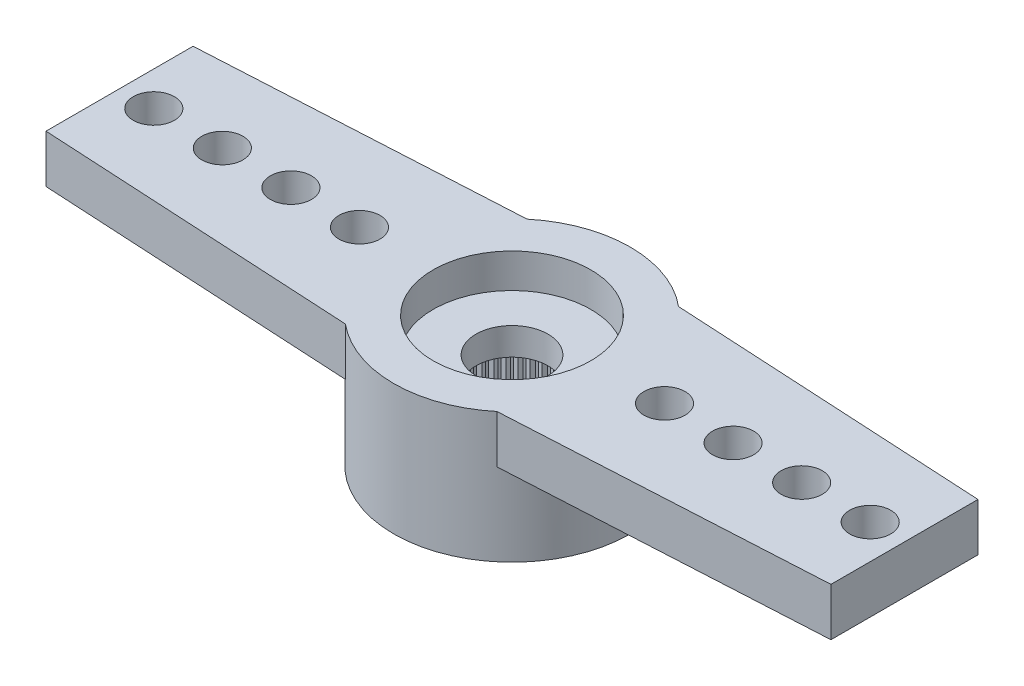
SolidWorks part; units mm, degrees
material "PVC Rígido"
ref_plane "Plano frontal" through (0, 0, 0) normal (0, 0, 1) x (1, 0, 0)
ref_plane "Plano superior" through (0, 0, 0) normal (0, 1, 0) x (1, 0, 0)
ref_plane "Plano direito" through (0, 0, 0) normal (1, 0, 0) x (0, 0, -1)
sketch "Esboço1" plane through (0, 0, 0) normal (0, 1, 0) x (1, 0, 0)
  line L0 (0, 0) -> (-14.05, 0) construction
  line L1 (-14.1591, 1.997) -> (-2.2091, 2.65)
  line L2 (-2.2091, -2.65) -> (-14.1591, -1.997)
  arc A0 (-2.2091, -2.65) -> (-2.2091, 2.65) centre (0, 0) ccw
  arc A1 (-14.1591, 1.997) -> (-14.1591, -1.997) centre (-14.05, 0) ccw
  dimension "D1" = 6.9
  dimension "D2" = 4
  dimension "D3" = 19.5
  dimension "D4" = 5.3
extrude "Ressalto-extrusão1" add sketch "Esboço1" against normal blind 1.4
sketch "Esboço2" plane through (0, -1.4, 0) normal (0, -1, 0) x (1, 0, 0)
  arc A0 (-2.2091, -2.65) -> (-2.2091, 2.65) centre (0, 0) ccw construction
  circle A1 centre (0, 0) radius 3.45
extrude "Ressalto-extrusão2" add sketch "Esboço2" along normal offset from surface (2.4 mm away) 3.8 up to face at (-7.242, 0, 0)
hole_wizard "Furo4" positions "Esboço9" profile "Esboço10" legacy end condition through all
sketch "Esboço9" plane through (0, 0, 0) normal (0, 1, 0) x (1, 0, 0)
  line L1 (-14.45, 0) -> (0, 0) construction
  arc A2 (-14.1591, 1.997) -> (-14.1591, -1.997) centre (-14.05, 0) ccw construction
  point P0 (-14.45, 0)
  point P19 (-16.05, 0)
  dimension "D1" = 1.6
sketch "Esboço10" plane through (-14.45, 0, 0) normal (1, 0, 0) x (0, 0, 1)
  line L0 (0, 0) -> (0, 3.8)
  line L1 (0, 3.8) -> (0.6, 3.8)
  line L2 (0.6, 3.8) -> (0.6, 0)
  line L3 (0.6, 0) -> (0, 0)
  line L4 (0, 110) -> (0, -10) construction
  dimension "Diameter" = 1.2
  dimension "Depth" = 3.8
pattern_linear "Padrão linear1" count 6 spacing 2 along (1, 0, 0) of "Furo4"
pattern_circular "PadrãoCircular2" count 2 over 360 about axis through (0, 0, 0) along (0, 1, 0) of "Ressalto-extrusão1", "Furo4", "Padrão linear1"
hole_wizard "Furo1" positions "Esboço3" profile "Esboço4" legacy
sketch "Esboço3" plane through (0, -3.8, 0) normal (0, -1, 0) x (-1, 0, 0)
  point P0 (0, 0)
sketch "Esboço4" plane through (0, -3.8, 0) normal (1, 0, 0) x (0, 0, -1)
  line L0 (0, 0) -> (0, 2)
  line L1 (0, 2) -> (2.475, 2)
  line L2 (2.475, 2) -> (2.475, 0)
  line L3 (2.475, 0) -> (0, 0)
  line L4 (0, 110) -> (0, -10) construction
  dimension "Diameter" = 4.95
  dimension "Depth" = 2
hole_wizard "Furo2" positions "Esboço5" profile "Esboço6" legacy
sketch "Esboço5" plane through (0, 0, 0) normal (0, 1, 0) x (1, 0, 0)
  point P0 (0, 0)
sketch "Esboço6" plane through (0, 0, 0) normal (1, 0, 0) x (0, 0, 1)
  line L0 (0, 0) -> (0, 1)
  line L1 (0, 1) -> (2.3, 1)
  line L2 (2.3, 1) -> (2.3, 0)
  line L3 (2.3, 0) -> (0, 0)
  line L4 (0, 110) -> (0, -10) construction
  dimension "Diameter" = 4.6
  dimension "Depth" = 1
hole_wizard "Furo3" positions "Esboço7" profile "Esboço8" legacy end condition through all
sketch "Esboço7" plane through (0, 0, 0) normal (0, 1, 0) x (1, 0, 0)
  point P0 (0, 0)
sketch "Esboço8" plane through (0, 0, 0) normal (1, 0, 0) x (0, 0, 1)
  line L0 (0, 0) -> (0, 3.8)
  line L1 (0, 3.8) -> (1.05, 3.8)
  line L2 (1.05, 3.8) -> (1.05, 0)
  line L3 (1.05, 0) -> (0, 0)
  line L4 (0, 110) -> (0, -10) construction
  dimension "Diameter" = 2.1
  dimension "Depth" = 3.8
sketch "Esboço11" plane through (0, -3.8, 0) normal (0, -1, 0) x (1, 0, 0)
  line L0 (-0.0981, 2.4731) -> (0, 2.375)
  line L1 (0, 2.375) -> (0.0981, 2.4731)
  line L2 (0, 0) -> (0, 2.475) construction
  circle A0 centre (0, 0) radius 2.375 construction
  circle A1 centre (0, 0) radius 2.475
  arc A2 (0.0981, 2.4731) -> (-0.0981, 2.4731) centre (0, 0) ccw
  dimension "D3" = 4.75
  dimension "D2" = 0.1
  dimension "D1" = 0
extrude "Ressalto-extrusão3" add sketch "Esboço11" against normal up to surface (2 mm away) up to face at (0, -1.8, 1.05)
pattern_circular "PadrãoCircular1" count 60 over 360 about axis through (0, 0, 0) along (0, 1, 0) of "Ressalto-extrusão3"
ref_plane "Plane1" through (-5.3014, 0, 5.5681) normal (0.6896, 0, -0.7242) x (0, 1, 0)
sketch "Sketch2" plane through (0, 0, 0) normal (0, 1, 0) x (1, 0, 0)
  line L0 (16.05, 0) -> (-16.05, 0)
  line L1 (-11.45, -2.1451) -> (-11.45, 2.1451)
  line L2 (-14.1591, -1.997) -> (-2.2091, -2.65) construction
  line L3 (-2.2091, 2.65) -> (-14.1591, 1.997) construction
  line L4 (0, 0) -> (0, 3.45)
  line L5 (11.45, -2.1451) -> (11.45, 2.1451)
  line L6 (-11.45, -2.1451) -> (-18.0748, -1.7831)
  line L7 (-18.0748, -1.7831) -> (-17.5014, 2.1451)
  line L8 (-17.5014, 2.1451) -> (-11.45, 2.1451)
  line L9 (11.45, -2.1451) -> (17.0395, -2.1451)
  line L10 (17.0395, -2.1451) -> (15.7214, 1.9429)
  line L11 (15.7214, 1.9429) -> (11.45, 2.1451)
  arc A0 (-14.1591, 1.997) -> (-14.1591, -1.997) centre (-14.05, 0) ccw construction
  circle A1 centre (-10.45, 0) radius 0.6 construction
  arc A2 (2.2091, 2.65) -> (-2.2091, 2.65) centre (0, 0) ccw construction
  spline S0 degree 3 poles (15.8563, 1.7298) (16.0716, 1.5248) (16.2539, 1.4345) (16.5085, 1.401) (16.5902, 1.4063) (16.7348, 1.4491) (16.7968, 1.486) (16.8931, 1.5875) (16.926, 1.6505) (16.9584, 1.7939) (16.9576, 1.874) (16.9052, 2.1202) (16.8011, 2.2948) (16.5884, 2.4973) (16.5082, 2.5555) (16.3412, 2.6437) (16.2556, 2.6734) (16.0879, 2.7003) (16.0088, 2.6969) (15.8673, 2.6572) (15.8057, 2.6206) (15.6627, 2.4702) (15.6242, 2.3121) (15.6703, 2.0595) (15.7024, 1.9726) (15.7958, 1.8073) (15.8563, 1.7298) (16.0716, 1.5248) (16.2539, 1.4345) knots -0.0625 -0.0625 0 0 0.125 0.125 0.1875 0.1875 0.25 0.25 0.3125 0.3125 0.375 0.375 0.5 0.5 0.5625 0.5625 0.625 0.625 0.6875 0.6875 0.75 0.75 0.875 0.875 0.9375 0.9375 1 1 1.125 1.125 1.1875 only from (15.9281, 1.6615) to (15.9281, 1.6615) construction
  circle M9 centre (12.45, 0) radius 0.6
  circle M10 centre (14.45, 0) radius 0.6
  line M11 (-14.1591, -1.997) -> (-2.2091, -2.65)
  line M13 (2.2091, -2.65) -> (14.1591, -1.997)
  arc M14 (14.1591, -1.997) -> (14.1591, 1.997) centre (14.05, 0) ccw
  line M15 (14.1591, 1.997) -> (2.2091, 2.65)
  line M17 (-2.2091, 2.65) -> (-14.1591, 1.997)
  arc M18 (-14.1591, 1.997) -> (-14.1591, -1.997) centre (-14.05, 0) ccw
  circle M19 centre (-12.45, 0) radius 0.6
  circle M20 centre (-14.45, 0) radius 0.6
  dimension "D1" = 90
  dimension "D2" = 1
extrude "Cut-Extrude2" cut sketch "Sketch2" against normal blind 10 contours L5 L0 M13 M14 M10 M9 | L8 L7 L6 M18 M17 | L0 L1 M17 M18 M20 M19 | L1 L0 M11 M19 M20 M18 | L5 L0 M9 M10 M14 M15
